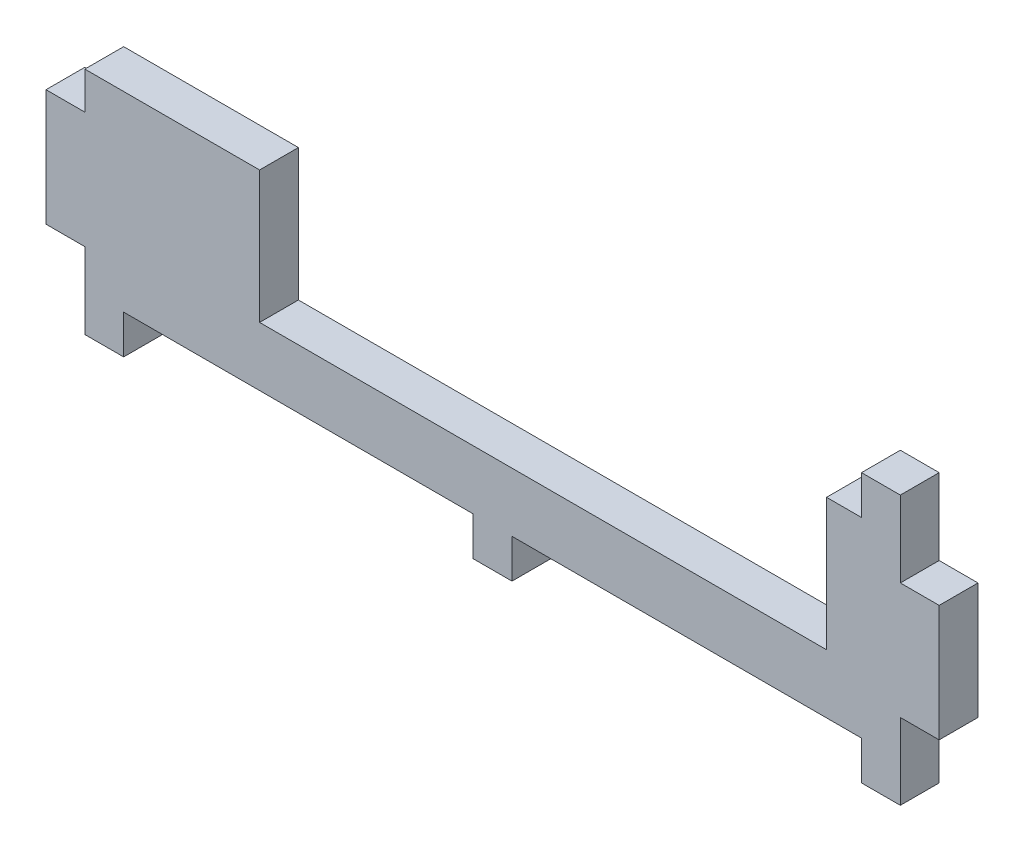
SolidWorks part; units mm, degrees
ref_plane "Front" through (0, 0, 0) normal (0, 0, 1) x (1, 0, 0)
ref_plane "Top" through (0, 0, 0) normal (0, 1, 0) x (1, 0, 0)
ref_plane "Right" through (0, 0, 0) normal (1, 0, 0) x (0, 0, -1)
sketch "Sketch1" plane through (0, 0, 0) normal (0, 0, 1) x (1, 0, 0)
  line L1 (-52.5, -6.15) -> (52.5, -6.15)
  line L2 (-52.5, -6.15) -> (-52.5, 6.15)
  line L3 (-52.5, 6.15) -> (52.5, 6.15)
  line L4 (52.5, -6.15) -> (52.5, 6.15)
  line L5 (-52.5, -6.15) -> (52.5, 6.15) construction
  line L6 (-52.5, 6.15) -> (52.5, -6.15) construction
  point P0 (0, 0)
  dimension "D1" = 12.3
  dimension "D2" = 105
extrude "Boss-Extrude1" add sketch "Sketch1" along normal blind 5
sketch "Sketch2" plane through (0, -6.15, 0) normal (0, -1, 0) x (1, 0, 0)
  line L0 (-52.5, 5) -> (52.5, 5) construction
  line L5 (-52.5, 0) -> (52.5, 0) construction
  line L7 (52.5, 5) -> (52.5, 0) construction
  line L11 (47.5, 5) -> (52.5, 5)
  line L12 (47.5, 5) -> (47.5, 0)
  line L13 (47.5, 0) -> (52.5, 0)
  line L14 (52.5, 5) -> (52.5, 0)
  dimension "D3" = 5
extrude "Boss-Extrude2" add sketch "Sketch2" along normal blind 5
mirror "Mirror1" about plane through (-52.5, 6.15, 5) normal (0, -1, 0) of bodies 102
sketch "Sketch3" plane through (0, 18.45, 0) normal (0, 1, 0) x (1, 0, 0)
  line L0 (-52.5, 0) -> (47.5, 0) construction
  line L1 (-30, 0) -> (43, 0)
  line L2 (-30, 0) -> (-30, -5)
  line L3 (-30, -5) -> (43, -5)
  line L4 (43, 0) -> (43, -5)
  line L5 (-52.5, -5) -> (47.5, -5) construction
  line L6 (-52.5, -5) -> (-52.5, 0) construction
  dimension "D1" = 73
  dimension "D2" = 22.5
extrude "Cut-Extrude1" cut sketch "Sketch3" against normal blind 17
sketch "Sketch4" plane through (0, -6.15, 0) normal (0, -1, 0) x (1, 0, 0)
  line L0 (-52.5, 5) -> (47.5, 5) construction
  line L1 (-2.5, 5) -> (2.5, 5)
  line L2 (-2.5, 5) -> (-2.5, 0)
  line L3 (-2.5, 0) -> (2.5, 0)
  line L4 (2.5, 5) -> (2.5, 0)
  line L5 (-52.5, 0) -> (47.5, 0) construction
  line L7 (47.5, 5) -> (47.5, 0) construction
  line L8 (-52.5, 0) -> (47.5, 0) construction
  line L9 (-52.5, 5) -> (-47.5, 5)
  line L10 (-52.5, 5) -> (-52.5, 0)
  line L11 (-52.5, 0) -> (-47.5, 0)
  line L12 (-47.5, 5) -> (-47.5, 0)
  dimension "D1" = 5
  dimension "D2" = 45
  dimension "D3" = 5
extrude "Boss-Extrude3" add sketch "Sketch4" along normal blind 5
sketch "Sketch5" plane through (-52.5, 0, 0) normal (-1, 0, 0) x (0, 0, 1)
  line L0 (0, 18.45) -> (0, -11.15) construction
  line L1 (0, 13.65) -> (5, 13.65)
  line L2 (0, 13.65) -> (0, -1.35)
  line L3 (0, -1.35) -> (5, -1.35)
  line L4 (5, 13.65) -> (5, -1.35)
  line L5 (5, 18.45) -> (5, -11.15) construction
  line L6 (5, 18.45) -> (0, 18.45) construction
  point P8 (2.5, 18.45)
  dimension "D1" = 15
  dimension "D2" = 4.8
extrude "Boss-Extrude4" add sketch "Sketch5" along normal blind 5
mirror "Mirror2" about plane through (0, 0, 0) normal (1, 0, 0) of "Boss-Extrude4"
